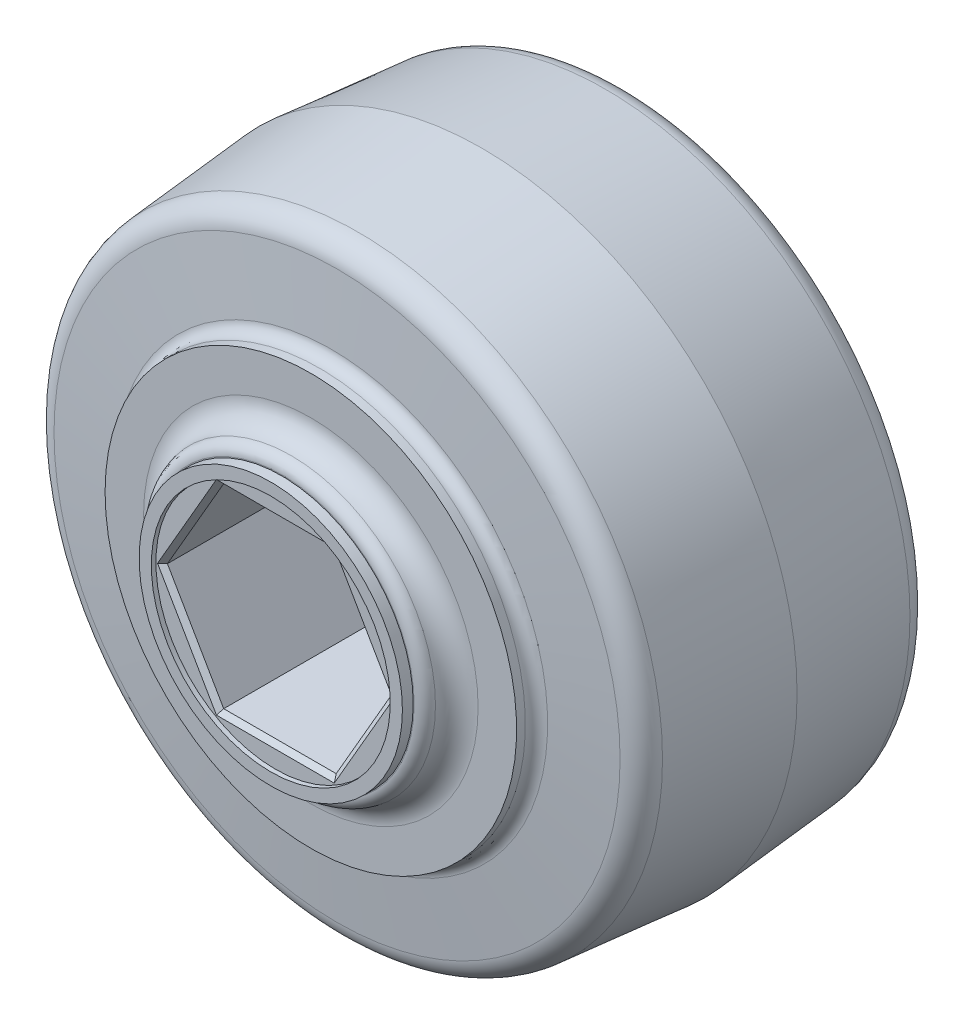
SolidWorks part; units mm, degrees
ref_plane "Front Plane" through (0, 0, 0) normal (0, 0, 1) x (1, 0, 0)
ref_plane "Top Plane" through (0, 0, 0) normal (0, 1, 0) x (1, 0, 0)
ref_plane "Right Plane" through (0, 0, 0) normal (1, 0, 0) x (0, 0, -1)
ref_plane "Plane1" through (0, 0, 0) normal (0, -1, 0) x (1, 0, 0)
sketch "Sketch1" plane through (0, 0, 0) normal (0, -1, 0) x (1, 0, 0)
  line L0 (9.4497, 13.0937) -> (0, 13.0937)
  line L1 (0, 13.0937) -> (0, -13.0937)
  line L2 (0, -13.0937) -> (9.4497, -13.0937)
  line L3 (10.922, -11.176) -> (13.4366, -11.176)
  line L4 (13.4366, -11.176) -> (13.4366, -9.906)
  line L5 (13.4366, -9.906) -> (19.7557, -9.3531)
  line L6 (19.7557, -9.3531) -> (20.574, 0)
  line L7 (20.574, 0) -> (19.7557, 9.3531)
  line L8 (19.7557, 9.3531) -> (13.4366, 9.906)
  line L9 (13.4366, 9.906) -> (13.4366, 11.176)
  line L10 (13.4366, 11.176) -> (10.922, 11.176)
  line L11 (0, 13.0937) -> (0, -13.0937) construction
  arc A0 (9.4497, -13.0937) -> (10.922, -11.176) centre (10.922, -12.7) cw
  arc A1 (10.922, 11.176) -> (9.4497, 13.0937) centre (10.922, 12.7) cw
revolve "Revolve1" add sketch "Sketch1" angle 360 about L11
sketch "Sketch2" plane through (0, 0, 13.0937) normal (0, 0, 1) x (1, 0, 0)
  circle A0 centre (0, 0) radius 8.6035
extrude "Boss-Extrude1" add sketch "Sketch2" along normal blind 0.7 draft 0.5
sketch "Sketch3" plane through (0, 0, -13.0937) normal (0, 0, -1) x (-1, 0, 0)
  circle A0 centre (0, 0) radius 8.6035
extrude "Boss-Extrude2" add sketch "Sketch3" along normal blind 0.7 draft 0.5
sketch "Sketch4" plane through (0, 0, -13.7937) normal (0, 0, -1) x (-1, 0, 0)
  line L0 (7.347, 0) -> (3.6735, 6.3627)
  line L1 (3.6735, 6.3627) -> (-3.6735, 6.3627)
  line L2 (-3.6735, 6.3627) -> (-7.347, 0)
  line L3 (-7.347, 0) -> (-3.6735, -6.3627)
  line L4 (-3.6735, -6.3627) -> (3.6735, -6.3627)
  line L5 (3.6735, -6.3627) -> (7.347, 0)
extrude "Cut-Extrude1" cut sketch "Sketch4" against normal through all
sketch "Sketch5" plane through (0, 0, 0) normal (1, 0, 0) x (0, 0, -1)
  line L0 (13.7937, 0) -> (13.7937, 7.8026)
  line L1 (13.7937, 7.8026) -> (13.4937, 7.8)
  line L2 (13.4937, 7.8) -> (13.4937, 0)
  line L3 (13.4937, 0) -> (13.7937, 0)
  line L4 (13.4937, 0) -> (13.7937, 0) construction
revolve "Cut-Revolve1" cut sketch "Sketch5" angle 360 about L4
sketch "Sketch6" plane through (0, 0, 0) normal (1, 0, 0) x (0, 0, -1)
  line L0 (-13.7937, 0) -> (-13.7937, -7.8026)
  line L1 (-13.7937, -7.8026) -> (-13.4937, -7.8)
  line L2 (-13.4937, -7.8) -> (-13.4937, 0)
  line L3 (-13.4937, 0) -> (-13.7937, 0)
  line L4 (-13.4937, 0) -> (-13.7937, 0) construction
revolve "Cut-Revolve2" cut sketch "Sketch6" angle 360 about L4
chamfer "Chamfer1" distance 0.3 angle 45 12 edges at (5.5103, -3.1813, 13.4937) (0, -6.3627, 13.4937) (5.5103, 3.1813, 13.4937) (-5.5103, -3.1814, 13.4937) (0, 6.3627, 13.4937) (-5.5103, 3.1813, 13.4937) (5.5103, 3.1813, -13.4937) (0, 6.3627, -13.4937) (5.5103, -3.1813, -13.4937) (-5.5103, 3.1813, -13.4937) (0, -6.3627, -13.4937) (-5.5103, -3.1814, -13.4937)
fillet "Fillet1" radius 0.762 4 edges at (-9.4497, 0, -13.0937) (-9.4497, 0, 13.0937) (-13.4366, 0, -9.906) (-13.4366, 0, 9.906)
fillet "Fillet2" radius 1.524 2 edges at (-19.7557, 0, -9.3531) (-19.7557, 0, 9.3531)
